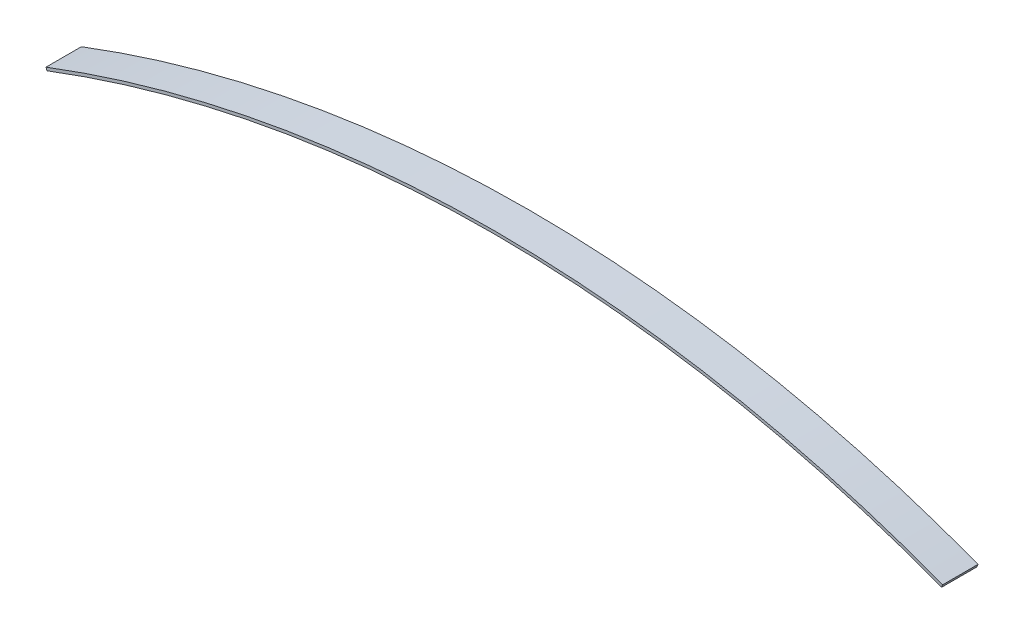
SolidWorks part; units mm, degrees
ref_plane "Front Plane" through (0, 0, 0) normal (0, 0, 1) x (1, 0, 0)
ref_plane "Top Plane" through (0, 0, 0) normal (0, 1, 0) x (1, 0, 0)
ref_plane "Right Plane" through (0, 0, 0) normal (1, 0, 0) x (0, 0, -1)
sketch "Sketch1" plane through (0, 0, 0) normal (0, 0, 1) x (1, 0, 0)
  line L0 (-1000, 2624.834) -> (0, 0) construction
  line L1 (0, 0) -> (1000, 2624.834) construction
  line L2 (0, 0) -> (-998.9069, 2621.9647) construction
  line L3 (0, 0) -> (-1001.1854, 2627.9453) construction
  line L4 (0, 0) -> (0, 2808.8705) construction
  arc A0 (-1000, 2624.834) -> (1000, 2624.834) centre (0, 0) cw
  point P3 (0, 2808.8705)
  dimension "D1" = 2000
  dimension "D2" = 20.856
  dimension "D3" = 2812.2
  dimension "D4" = 2805.8
ref_plane "Plane1" through (0, 0, 0) normal (0, 0, 1) x (1, 0, 0)
ref_plane "Plane2" through (0, 0, 0) normal (-0.9345, -0.356, 0) x (0.356, -0.9345, 0)
sketch "Sketch2" plane through (0, 0, 0) normal (-0.9345, -0.356, 0) x (0.356, -0.9345, 0)
  line L0 (-2808.8705, 0) -> (0, 0) construction
  line L1 (-2812.2, 39.5) -> (-2805.8, 39.5)
  line L2 (-2812.2, 39.5) -> (-2812.2, -39.5)
  line L3 (-2812.2, -39.5) -> (-2805.8, -39.5)
  line L4 (-2805.8, 39.5) -> (-2805.8, -39.5)
  line L7 (-2096.8405, 0) -> (-2808.8705, 0) construction
  point P0 (-2808.8705, 0)
  point P9 (-2805.8, 0)
  dimension "D3" = 79
sweep "Sweep1" add profiles "Sketch2" path "Sketch1"
equation "\"theta\"= .3640 * 180 / pi"
equation "\"a\" = 2.8058"
equation "\"b\" = .0790"
equation "\"c\" = 2.8122"
equation "\"D2@Sketch1\"= \"theta\""
equation "\"D3@Sketch2\"=\"b\""
equation "\"D3@Sketch1\"=\"c\""
equation "\"D4@Sketch1\"=\"a\""
equation "\"span\"= 2"
equation "\"D1@Sketch1\"=\"span\""
